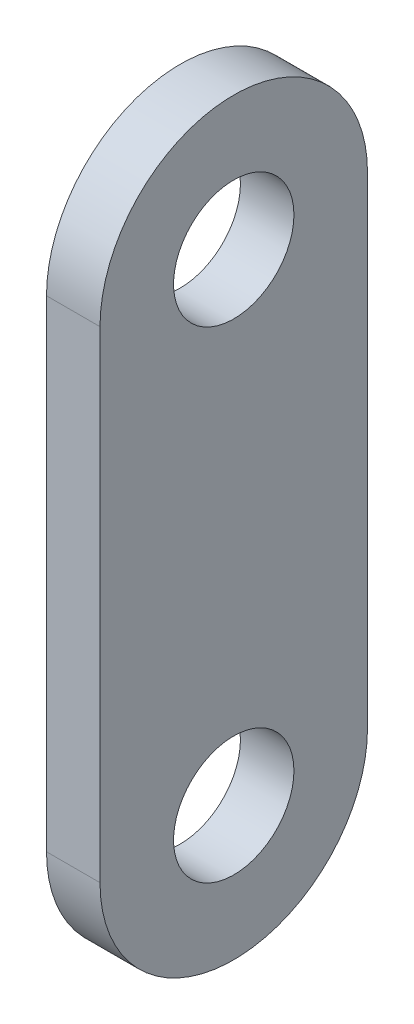
SolidWorks part; units mm, degrees
ref_plane "Front Plane" through (0, 0, 0) normal (0, 0, 1) x (1, 0, 0)
ref_plane "Top Plane" through (0, 0, 0) normal (0, 1, 0) x (1, 0, 0)
ref_plane "Right Plane" through (0, 0, 0) normal (1, 0, 0) x (0, 0, -1)
sketch "Sketch1" plane through (0, 0, 0) normal (1, 0, 0) x (0, 0, -1)
  line L0 (0, -28.575) -> (0, 28.575) construction
  line L1 (-15.875, -28.575) -> (-15.875, 28.575)
  line L2 (15.875, -28.575) -> (15.875, 28.575)
  arc A0 (-15.875, -28.575) -> (15.875, -28.575) centre (0, -28.575) ccw
  arc A1 (15.875, 28.575) -> (-15.875, 28.575) centre (0, 28.575) ccw
  point P2 (0, 0)
  dimension "D1" = 15.875
  dimension "D2" = 57.15
extrude "Boss-Extrude1" add sketch "Sketch1" along normal mid plane 6.35
sketch "Sketch2" plane through (3.175, 0, 0) normal (1, 0, 0) x (0, 0, -1)
  circle A0 centre (0, 28.575) radius 7.1438
  circle A1 centre (0, -28.575) radius 7.1438
  dimension "D1" = 14.2875
extrude "Cut-Extrude1" cut sketch "Sketch2" against normal up to next
